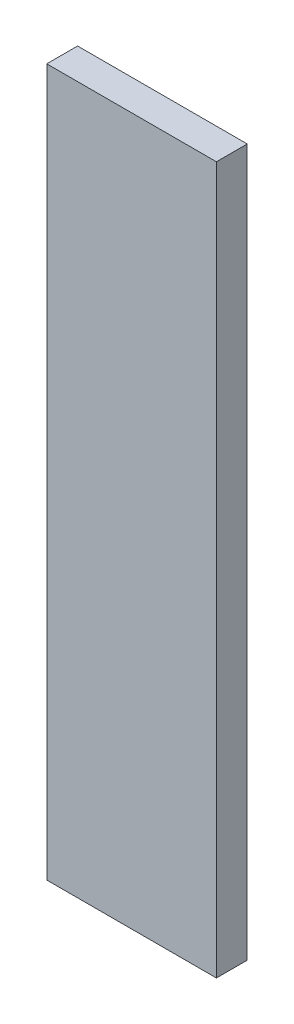
SolidWorks part; units mm, degrees
ref_plane "Front Plane" through (0, 0, 0) normal (0, 0, 1) x (1, 0, 0)
ref_plane "Top Plane" through (0, 0, 0) normal (0, 1, 0) x (1, 0, 0)
ref_plane "Right Plane" through (0, 0, 0) normal (1, 0, 0) x (0, 0, -1)
sketch "Sketch1" plane through (0, 0, 0) normal (0, 0, 1) x (1, 0, 0)
  line L1 (-23, 0) -> (43, 0)
  line L2 (-23, 0) -> (-23, 275)
  line L3 (-23, 275) -> (43, 275)
  line L4 (43, 0) -> (43, 275)
  line L5 (23, 255) -> (-23, 255)
  line L6 (23, 255) -> (23, 0)
  line L7 (23, 0) -> (-23, 0)
  line L8 (-23, 255) -> (-23, 0)
  dimension "D1" = 20
  dimension "D2" = 20
extrude "Boss-Extrude1" add sketch "Sketch1" against normal blind 6 contours L5 L6 L1 L4 L3 L2
sketch "Sketch2" plane through (0, 0, 0) normal (0, 0, 1) x (1, 0, 0)
  line L1 (43, 275) -> (-23, 275)
  line L2 (43, 275) -> (43, 0)
  line L3 (43, 0) -> (-23, 0)
  line L4 (-23, 275) -> (-23, 0)
extrude "Boss-Extrude2" add sketch "Sketch2" along normal blind 6
sketch "Sketch3" plane through (0, 0, -6) normal (0, 0, -1) x (-1, 0, 0)
  circle A0 centre (-23, 255) radius 10
  dimension "D1" = 20
extrude "Cut-Extrude1" cut sketch "Sketch3" against normal up to surface (6 mm away) up to face at (0, 127.5, 0)
